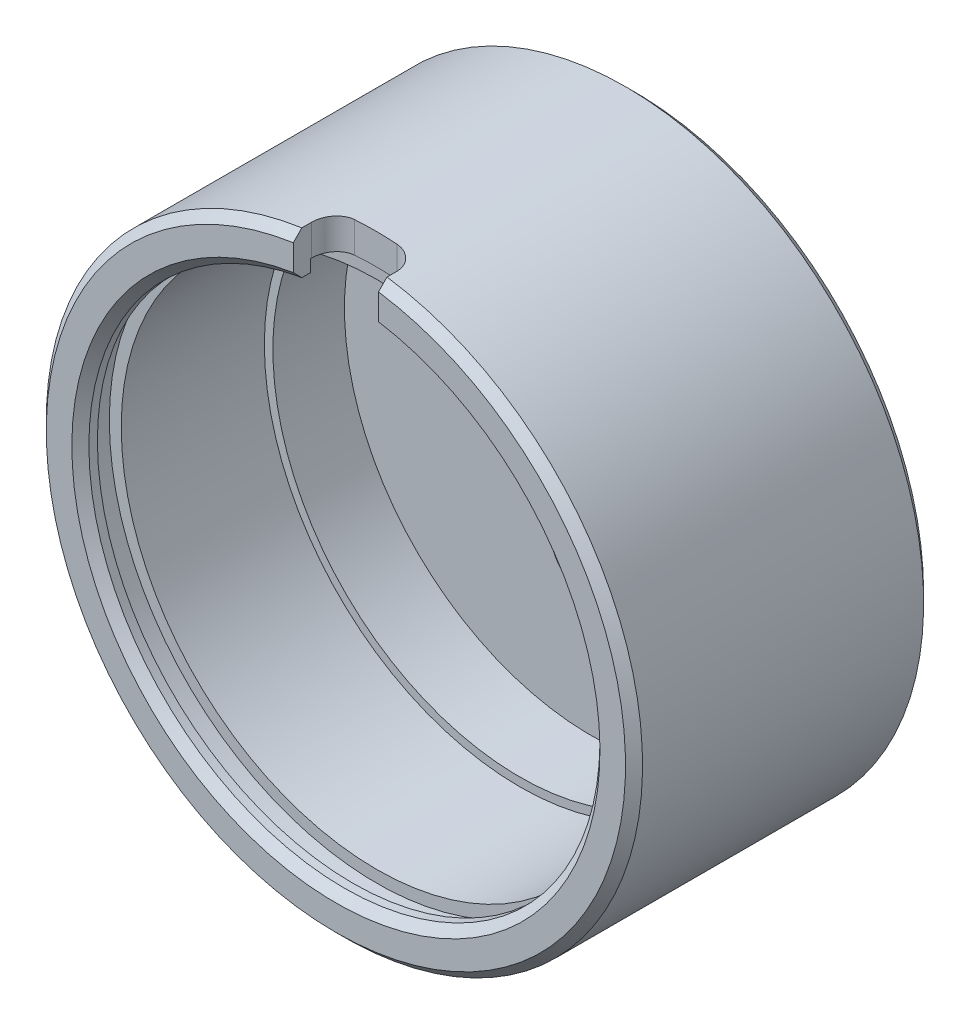
SolidWorks part; units mm, degrees
material "6061-T6 (SS)"
ref_plane "Front" through (0, 0, 0) normal (0, 0, 1) x (1, 0, 0)
ref_plane "Top" through (0, 0, 0) normal (0, 1, 0) x (1, 0, 0)
ref_plane "Right" through (0, 0, 0) normal (1, 0, 0) x (0, 0, -1)
sketch "Sketch1" plane through (0, 0, 0) normal (1, 0, 0) x (0, 0, -1)
  line L0 (-77.4032, 0) -> (89.9695, 0) construction
  line L1 (10.16, 0) -> (16.51, 0)
  line L2 (16.51, 0) -> (16.51, -44.45)
  line L3 (16.51, -44.45) -> (-27.94, -44.45)
  line L4 (-27.94, -44.45) -> (-27.94, -38.1)
  line L5 (-27.94, -38.1) -> (-25.4, -38.1)
  line L6 (-25.4, -38.1) -> (-25.4, -39.878)
  line L7 (-25.4, -39.878) -> (-21.844, -39.878)
  line L8 (-21.844, -39.878) -> (-21.844, -38.1)
  line L9 (-21.844, -38.1) -> (-0.508, -38.1)
  line L10 (-0.508, -38.1) -> (-0.508, -36.83)
  line L11 (-0.508, -36.83) -> (10.16, -36.83)
  line L12 (10.16, -36.83) -> (10.16, 0)
  dimension "D1" = 44.45
  dimension "D2" = 38.1
  dimension "D3" = 6.35
  dimension "D4" = 27.432
  dimension "D5" = 38.1
  dimension "D6" = 3.556
  dimension "D7" = 1.778
  dimension "D8" = 36.83
  dimension "D9" = 2.54
revolve "Revolve1" add sketch "Sketch1" angle 360 about L0
ref_plane "Plane1" through (0, 44.45, 0) normal (0, 1, 0) x (1, 0, 0)
sketch "Sketch2" plane through (0, 44.45, 0) normal (0, 1, 0) x (1, 0, 0)
  line L0 (-44.45, -27.94) -> (44.45, -27.94) construction
  line L1 (-6.35, -27.94) -> (6.35, -27.94)
  line L2 (-6.35, -27.94) -> (-6.35, -25.1968)
  line L3 (-3.175, -22.0218) -> (3.175, -22.0218)
  line L4 (6.35, -27.94) -> (6.35, -25.1968)
  arc A0 (3.175, -22.0218) -> (6.35, -25.1968) centre (3.175, -25.1968) cw
  arc A1 (-3.175, -22.0218) -> (-6.35, -25.1968) centre (-3.175, -25.1968) ccw
  point P6 (0, -27.94)
  point P12 (-6.35, -22.0218)
  dimension "D3" = 3.175
  dimension "D1" = 5.9182
  dimension "D2" = 12.7
extrude "Cut-Extrude1" cut sketch "Sketch2" against normal up to next
sketch "Sketch3" plane through (0, 0, -16.51) normal (0, 0, -1) x (-1, 0, 0)
  circle A0 centre (-24.13, 0) radius 12.7
  dimension "D1" = 25.4
  dimension "D2" = 24.13
extrude "Cut-Extrude2" [suppressed] cut sketch "Sketch3" against normal blind 1.27
sketch "Sketch6" [suppressed] plane through (0, 0, -15.24) normal (0, 0, -1) x (-1, 0, 0)
  circle A0 centre (-24.13, 0) radius 12.7 construction
  circle A1 centre (-24.13, 0) radius 12.7
hole_wizard "Ø1.0mm Dowel Hole1" [suppressed] positions "Sketch7" profile "Sketch8" hole size "Ø1.0" standard "ANSI Metric"
sketch "Sketch7" [suppressed] plane through (0, 0, -15.24) normal (0, 0, -1) x (-1, 0, 0)
  point P0 (-24.13, 0)
sketch "Sketch8" plane through (24.13, 0, -15.24) normal (1, 0, 0) x (0, 1, 0)
  line L0 (0, 0) -> (0, 43.18)
  line L1 (0, 43.18) -> (5.75, 43.18)
  line L2 (5.75, 43.18) -> (5.75, 0)
  line L5 (5.75, 0) -> (0, 0)
  line L11 (0, -6.35) -> (0, 107.95) construction
  dimension "Thru Hole Dia." = 11.5
  dimension "Thru Hole Depth" = 43.18
chamfer "Chamfer2" distance 1.27 angle 45 2 edges at (0, -44.45, 27.94) (44.45, 0, -16.51)
chamfer "Chamfer3" distance 1.27 angle 45 1 edges at (0, -38.1, 27.94)
hole_wizard "#38 (0.1015) Diameter Hole1" positions "Sketch9" profile "Sketch10" hole size "#38" standard "ANSI Inch"
sketch "Sketch9" plane through (0, 0, -10.16) normal (0, 0, 1) x (1, 0, 0)
  point P0 (0, 0)
sketch "Sketch10" plane through (0, 0, -10.16) normal (1, 0, 0) x (0, -1, 0)
  line L0 (0, 0) -> (0, 1.0285)
  line L1 (0, 1.0285) -> (1.2891, 0.254)
  line L2 (1.2891, 0.254) -> (1.289, 0)
  line L5 (1.289, 0) -> (0, 0)
  line L10 (0, 1.0285) -> (-1.2891, 0.254) construction
  line L11 (0, -6.35) -> (0, 107.95) construction
  dimension "Hole Dia." = 2.5781
  dimension "Hole Depth" = 0.254
  dimension "Drill Angle" = 118
hole_wizard "CBORE for 3/8 Binding Head Machine Screw1" positions "Sketch11" profile "Sketch12" counterbore size "3/8" standard "ANSI Inch" end condition up to next
sketch "Sketch11" plane through (0, 0, -16.51) normal (0, 0, -1) x (-1, 0, 0)
  point P0 (-24.1351, 0)
  dimension "D1" = 24.1351
sketch "Sketch12" plane through (24.1351, 0, -16.51) normal (1, 0, 0) x (0, 1, 0)
  line L0 (0, 0) -> (0, 6.35)
  line L1 (0, 6.35) -> (5.1562, 6.35)
  line L3 (5.1562, 6.35) -> (5.1562, 1.016)
  line L4 (5.1562, 1.016) -> (9.525, 1.016)
  line L5 (9.525, 1.016) -> (9.525, 0)
  line L7 (9.525, 0) -> (0, 0)
  line L11 (0, -6.35) -> (0, 107.95) construction
  dimension "Thru Hole Dia." = 10.3124
  dimension "Thru Hole Depth" = 6.35
  dimension "C'Bore Dia." = 19.05
  dimension "C'Bore Depth" = 1.016
sketch "Sketch15" plane through (0, 0, 0) normal (0, 0, 1) x (1, 0, 0)
  line L1 (-16.51, -16.51) -> (16.51, -16.51)
  line L2 (-16.51, -16.51) -> (-16.51, 16.51)
  line L3 (-16.51, 16.51) -> (16.51, 16.51)
  line L4 (16.51, -16.51) -> (16.51, 16.51)
  line L5 (0, 16.51) -> (0, -16.51) construction
  line L6 (-16.51, 0) -> (16.51, 0) construction
  circle A0 centre (16.51, -16.51) radius 4.445
  circle A1 centre (-16.51, -16.51) radius 4.445
  circle A2 centre (-16.51, 16.51) radius 4.445
  circle A3 centre (16.51, 16.51) radius 4.445
  point P0 (-16.51, 16.51)
  point P2 (16.51, 16.51)
  point P3 (-16.51, -16.51)
  point P5 (16.51, -16.51)
  dimension "D2" = 8.89
  dimension "D1" = 33.02
sketch "Sketch16" plane through (0, 0, -16.51) normal (0, 0, -1) x (-1, 0, 0)
  circle A0 centre (0.8009, -13.9328) radius 5.207
  circle A1 centre (6.3323, 14.1088) radius 3.3
  circle A3 centre (-24.1351, 0) radius 5.1562 construction
  dimension "D1" = 18.2013
  dimension "D5" = 6.6
  dimension "D2" = 25.1195
  dimension "D3" = 28.582
  dimension "D4" = 10.414
extrude "Cut-Extrude3" cut sketch "Sketch16" against normal up to next
